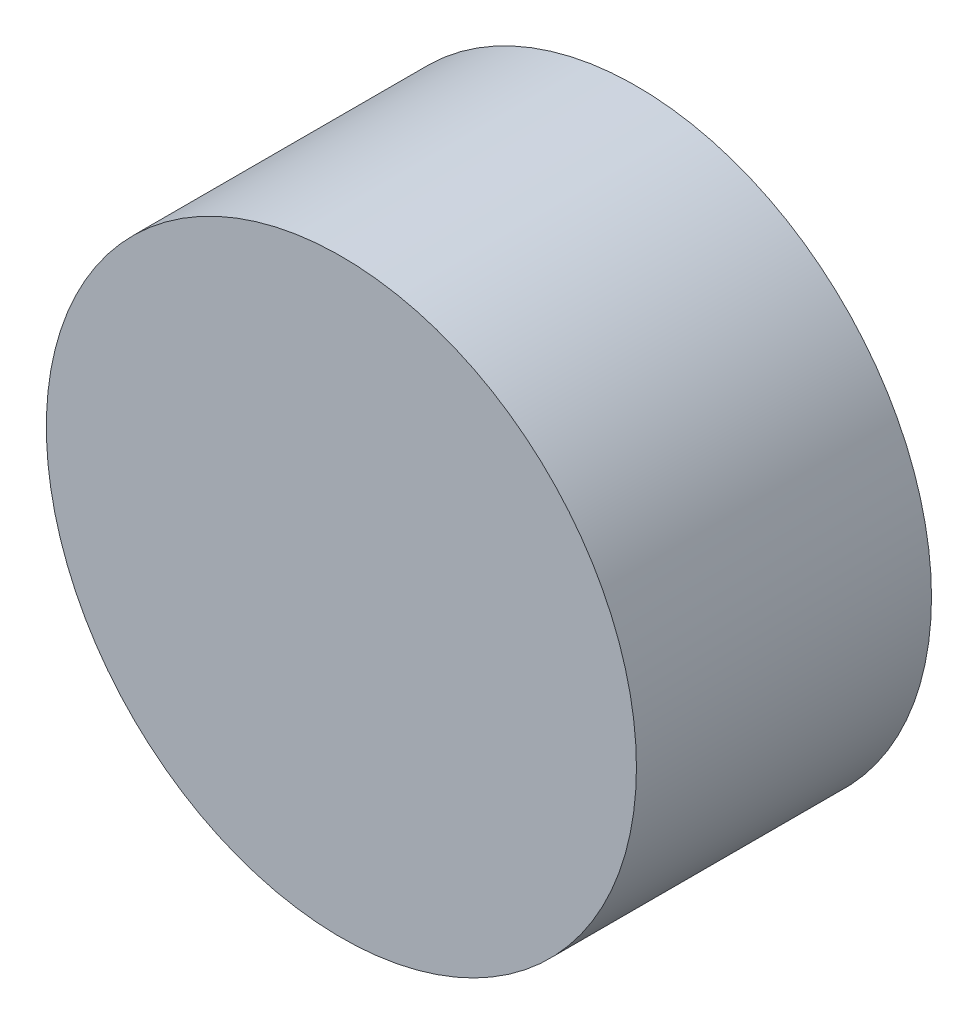
SolidWorks part; units mm, degrees
ref_plane "Front" through (0, 0, 0) normal (0, 0, 1) x (1, 0, 0)
ref_plane "Top" through (0, 0, 0) normal (0, 1, 0) x (1, 0, 0)
ref_plane "Right" through (0, 0, 0) normal (1, 0, 0) x (0, 0, -1)
sketch "Sketch1" plane through (0, 0, 0) normal (0, 0, 1) x (1, 0, 0)
  circle A0 centre (0, 0) radius 9.525
  dimension "D1" = 19.05
extrude "Boss-Extrude1" add sketch "Sketch1" along normal blind 9.525
